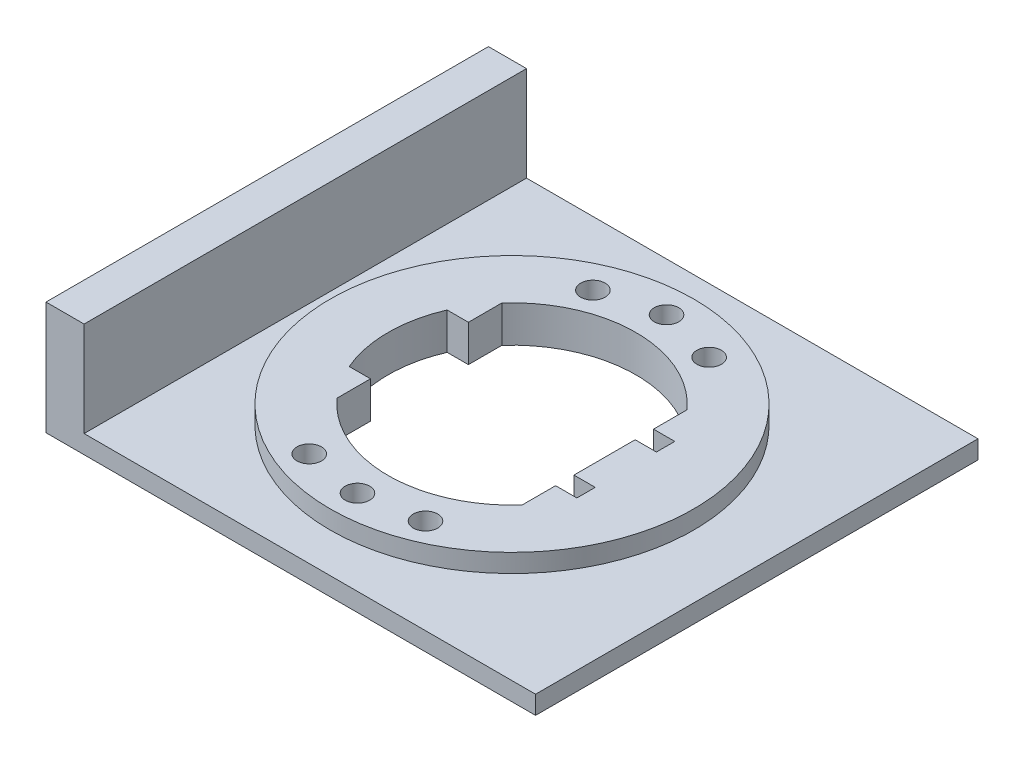
SolidWorks part; units mm, degrees
ref_plane "Front Plane" through (0, 0, 0) normal (0, 0, 1) x (1, 0, 0)
ref_plane "Top Plane" through (0, 0, 0) normal (0, 1, 0) x (1, 0, 0)
ref_plane "Right Plane" through (0, 0, 0) normal (1, 0, 0) x (0, 0, -1)
sketch "Sketch1" plane through (0, 0, 0) normal (0, 1, 0) x (1, 0, 0)
  line L1 (-38.4533, 1.5101) -> (41.5467, 1.5101)
  line L2 (-38.4533, 1.5101) -> (-38.4533, 73.8101)
  line L3 (-38.4533, 73.8101) -> (41.5467, 73.8101)
  line L4 (41.5467, 1.5101) -> (41.5467, 73.8101)
  dimension "D1" = 72.3
  dimension "D2" = 80
extrude "Boss-Extrude1" add sketch "Sketch1" along normal blind 6
sketch "Sketch2" plane through (0, 6, 0) normal (0, 1, 0) x (-1, 0, 0)
  line L0 (38.4533, -1.5101) -> (-41.5467, -1.5101) construction
  line L2 (38.4533, -73.8101) -> (38.4533, -1.5101) construction
  line L4 (38.4533, -73.8101) -> (-41.5467, -73.8101)
  line L5 (38.4533, -73.8101) -> (38.4533, -1.5101)
  line L6 (38.4533, -1.5101) -> (-41.5467, -1.5101)
  line L7 (-41.5467, -73.8101) -> (-41.5467, -1.5101)
  circle A0 centre (-1.5467, -37.6601) radius 29.705
  dimension "D1" = 59.41
  dimension "D2" = 36.15
  dimension "D3" = 40
extrude "Cut-Extrude1" cut sketch "Sketch2" against normal blind 3
sketch "Sketch3" plane through (0, 6, 0) normal (0, 1, 0) x (-1, 0, 0)
  line L1 (13.578, -51.1251) -> (-16.6713, -51.1251)
  line L2 (13.578, -51.1251) -> (13.578, -24.1951)
  line L3 (13.578, -24.1951) -> (-16.6713, -24.1951)
  line L4 (-16.6713, -51.1251) -> (-16.6713, -24.1951)
  line L5 (17.0561, -29.6601) -> (-20.1494, -29.6601)
  line L6 (17.0561, -29.6601) -> (17.0561, -45.6601)
  line L7 (17.0561, -45.6601) -> (-20.1494, -45.6601)
  line L8 (-20.1494, -29.6601) -> (-20.1494, -45.6601)
  line L9 (-20.1494, -29.6601) -> (-16.6713, -29.6601)
  line L10 (-20.1494, -29.6601) -> (-20.1494, -32.6601)
  line L11 (-20.1494, -32.6601) -> (-16.6713, -32.6601)
  line L12 (-16.6713, -29.6601) -> (-16.6713, -32.6601)
  line L13 (-20.1494, -45.6601) -> (-16.6713, -45.6601)
  line L14 (-20.1494, -45.6601) -> (-20.1494, -42.6601)
  line L15 (-20.1494, -42.6601) -> (-16.6713, -42.6601)
  line L16 (-16.6713, -45.6601) -> (-16.6713, -42.6601)
  circle A0 centre (-1.5467, -37.6601) radius 20.25
  dimension "D1" = 26.93
  dimension "D2" = 40.5
  dimension "D3" = 16
  dimension "D4" = 3
  dimension "D5" = 3
extrude "Cut-Extrude3" cut sketch "Sketch3" against normal through all contours L2 A0 | L4 L1 L2 L3 | L6 A0 | L15 L8 L7 L4 | L8 L11 L4 L5 | L2 L7 L4 L1 | L1 A0 | L5 L2 L3 L4 | L3 A0
sketch "Sketch5" plane through (0, 6, 0) normal (0, 1, 0) x (-1, 0, 0)
  circle A0 centre (-1.5467, -12.4101) radius 2
  circle A1 centre (-1.5467, -62.9101) radius 2
  arc A2 (13.578, -24.1951) -> (-16.6713, -24.1951) centre (-1.5467, -37.6601) ccw construction
  arc A3 (-16.6713, -51.1251) -> (13.578, -51.1251) centre (-1.5467, -37.6601) ccw construction
  point P4 (-1.5467, -17.4101)
  point P8 (-1.5467, -57.9101)
  point P12 (-1.5467, -17.4101)
  point P13 (-1.5467, -57.9101)
  dimension "D1" = 4
  dimension "D2" = 4
  dimension "D3" = 5
  dimension "D4" = 5
  dimension "D5" = 0
  dimension "D6" = 0
extrude "Cut-Extrude4" cut sketch "Sketch5" against normal through all
sketch "Sketch6" plane through (0, 6, 0) normal (0, 1, 0) x (1, 0, 0)
  circle A0 centre (-7.9533, 60.3766) radius 2
  circle A1 centre (11.0467, 60.3766) radius 2
  circle A2 centre (11.0467, 14.0266) radius 2
  circle A3 centre (-7.9533, 14.0266) radius 2
  arc A4 (16.6713, 51.1251) -> (-13.578, 51.1251) centre (1.5467, 37.6601) ccw construction
  point P8 (1.5467, 57.9101)
  dimension "D1" = 4
  dimension "D2" = 4
  dimension "D3" = 4
  dimension "D4" = 4
  dimension "D10" = 46.35
  dimension "D5" = 19
  dimension "D6" = 0
  dimension "D7" = 9.5
  dimension "D11" = 0
extrude "Cut-Extrude5" cut sketch "Sketch6" against normal through all
sketch "Sketch8" plane through (0, 3, 0) normal (0, 1, 0) x (1, 0, 0)
  line L0 (-38.4533, 1.5101) -> (41.5467, 1.5101) construction
  line L1 (-38.4533, 73.8101) -> (-32.2276, 73.8101)
  line L2 (-38.4533, 73.8101) -> (-38.4533, 1.5101)
  line L3 (-38.4533, 1.5101) -> (-32.2276, 1.5101)
  line L4 (-32.2276, 73.8101) -> (-32.2276, 1.5101)
extrude "Boss-Extrude2" add sketch "Sketch8" along normal blind 15.5
